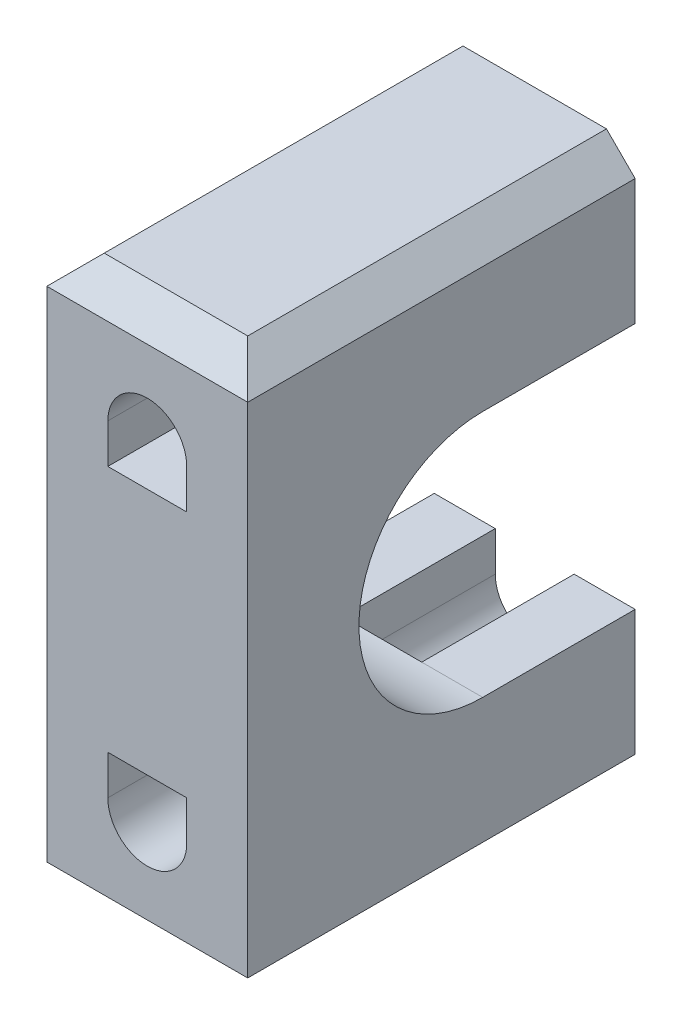
SolidWorks part; units mm, degrees
ref_plane "Front Plane" through (0, 0, 0) normal (0, 0, 1) x (1, 0, 0)
ref_plane "Top Plane" through (0, 0, 0) normal (0, 1, 0) x (1, 0, 0)
ref_plane "Right Plane" through (0, 0, 0) normal (1, 0, 0) x (0, 0, -1)
sketch "Sketch1" plane through (0, 0, 0) normal (0, 0, 1) x (1, 0, 0)
  line L0 (0, 11.375) -> (0, -11.375) construction
  line L1 (-2.75, 11.375) -> (-2.75, 8.625)
  line L2 (-7, 19.375) -> (7, 19.375)
  line L3 (-7, 19.375) -> (-7, -19.375)
  line L4 (-7, -19.375) -> (7, -19.375)
  line L5 (7, 19.375) -> (7, -19.375)
  line L6 (2.75, 11.375) -> (2.75, 8.625)
  line L7 (2.75, 8.625) -> (-2.75, 8.625)
  line L8 (-2.75, -11.375) -> (-2.75, -8.625)
  line L9 (2.75, -11.375) -> (2.75, -8.625)
  line L10 (2.75, -8.625) -> (-2.75, -8.625)
  circle A0 centre (0, 11.375) radius 2.75
  circle A1 centre (0, -11.375) radius 2.75
  point P4 (0, 0)
  point P5 (0, -11.125)
  point P7 (0, 11.125)
  point P13 (0, 19.375)
  point P14 (-7, 0)
  point P15 (0, -8.625)
  point P16 (0, 8.625)
  dimension "D2" = 5.5
  dimension "D3" = 0.25
  dimension "D4" = 0.25
  dimension "D5" = 14
  dimension "D6" = 8
  dimension "D1" = 17.25
extrude "Boss-Extrude1" add sketch "Sketch1" along normal blind 27
sketch "Sketch2" plane through (-7, 0, 0) normal (-1, 0, 0) x (0, 0, 1)
  line L0 (10.625, 8.625) -> (0, 8.625)
  line L1 (0, 19.375) -> (0, -19.375) construction
  line L2 (0, 8.625) -> (0, 0)
  line L3 (0, 0) -> (0, -8.625)
  line L4 (0, -8.625) -> (10.625, -8.625)
  circle A0 centre (10.625, 0) radius 8.625
  point P2 (0, 0)
  point P16 (2, 0)
  dimension "D1" = 17.25
  dimension "D2" = 2
extrude "Cut-Extrude1" cut sketch "Sketch2" against normal through all contours A0 L0 L4 M11 | A0
chamfer "Chamfer1" distance 2 angle 45 4 edges at (-7, -19.375, 13.5) (7, -19.375, 13.5) (-7, 19.375, 13.5) (7, 19.375, 13.5)
chamfer "Chamfer2" distance 2 angle 45 2 edges at (0, -19.375, 27) (0, 19.375, 27)
equation "\"D4@Sketch1\"=\"D3@Sketch1\""
